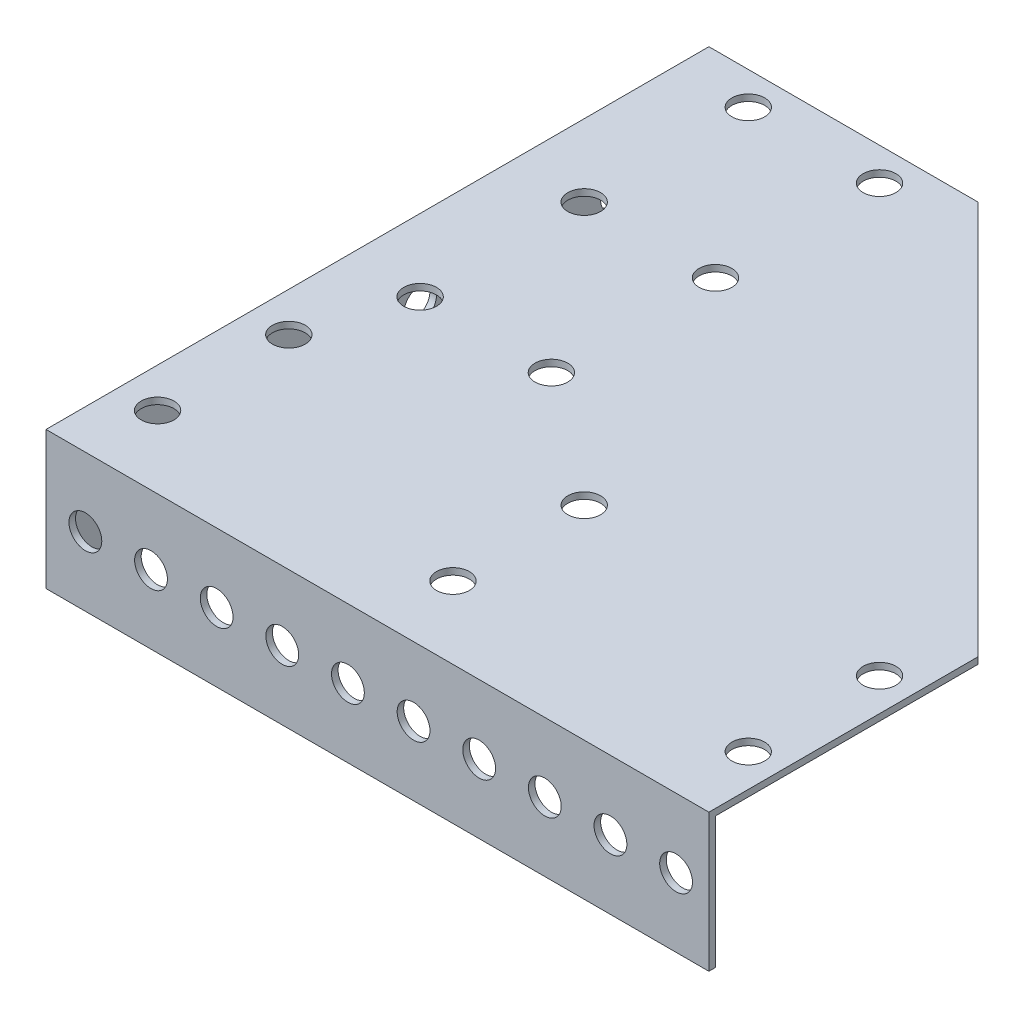
SolidWorks part; units mm, degrees
ref_plane "Front Plane" through (0, 0, 0) normal (0, 0, 1) x (1, 0, 0)
ref_plane "Top Plane" through (0, 0, 0) normal (0, 1, 0) x (1, 0, 0)
ref_plane "Right Plane" through (0, 0, 0) normal (1, 0, 0) x (0, 0, -1)
sketch "Sketch1" plane through (0, 0, 0) normal (0, 1, 0) x (1, 0, 0)
  line L0 (0, 0) -> (0, -100)
  line L1 (0, -100) -> (100, -100)
  line L2 (100, -100) -> (100, -60)
  line L3 (100, -60) -> (40, 0)
  line L4 (40, 0) -> (0, 0)
  line L5 (40, 0) -> (40, -60) construction
  line L6 (40, -60) -> (100, -60) construction
  line L7 (40, -5) -> (20, -5) construction
  line L8 (20, -5) -> (0, -5) construction
  line L9 (40, -30) -> (0, -30) construction
  line L10 (50, -80) -> (50, -60) construction
  line L11 (40, -5) -> (40, -30) construction
  line L12 (40, -17.5) -> (0, -17.5) construction
  line L13 (100, -80) -> (50, -80) construction
  line L14 (50, -100) -> (50, -80) construction
  circle A0 centre (10, -5) radius 2.5
  circle A1 centre (30, -5) radius 2.5
  circle A6 centre (30, -55) radius 2.5
  circle A7 centre (10, -55) radius 2.5
  circle A10 centre (30, -30) radius 2.5
  circle A11 centre (10, -30) radius 2.5
  circle A14 centre (50, -70) radius 2.5
  circle A15 centre (50, -90) radius 2.5
  circle A16 centre (95, -70) radius 2.5
  circle A17 centre (95, -90) radius 2.5
  circle A18 centre (5, -70) radius 2.5
  circle A19 centre (5, -90) radius 2.5
  dimension "D4" = 5
  dimension "D6" = 5
  dimension "D1" = 40
  dimension "D2" = 40
  dimension "D3" = 100
  dimension "D5" = 5
extrude "Boss-Extrude1" add sketch "Sketch1" along normal blind 1
sketch "Sketch2" plane through (0, 0, 0) normal (-1, 0, 0) x (0, 0, 1)
  line L0 (0, 0) -> (100, 0) construction
  line L9 (100, 1) -> (0, 1)
  line L10 (100, 1) -> (100, -20)
  line L11 (100, -20) -> (0, -20)
  line L12 (0, 1) -> (0, -20)
  line L13 (0, 1) -> (0, 0) construction
  line L14 (5, -10) -> (15, -10) construction
  line L15 (5, -10) -> (0, -10) construction
  line L16 (75, -10) -> (80, -10) construction
  line L17 (80, 0) -> (80, -20) construction
  circle A0 centre (5, -10) radius 2.5
  circle A1 centre (15, -10) radius 2.5
  circle A2 centre (25, -10) radius 2.5
  circle A3 centre (35, -10) radius 2.5
  circle A4 centre (45, -10) radius 2.5
  circle A5 centre (55, -10) radius 2.5
  circle A6 centre (65, -10) radius 2.5
  circle A7 centre (75, -10) radius 2.5
  dimension "D4" = 5
  dimension "D1" = 20
  dimension "D3" = 10
  dimension "D5" = 20
  dimension "D2" = 8
extrude "Boss-Extrude2" add sketch "Sketch2" along normal blind 1
sketch "Sketch3" plane through (0, 0, 100) normal (0, 0, 1) x (1, 0, 0)
  line L0 (95, -9.5) -> (85, -9.5) construction
  line L1 (100, 1) -> (-1, 1)
  line L2 (100, 1) -> (100, -20)
  line L3 (100, -20) -> (-1, -20)
  line L4 (-1, 1) -> (-1, -20)
  line L5 (-1, -20) -> (-1, 1) construction
  line L6 (-1, -20) -> (0, -20) construction
  line L7 (95, -9.5) -> (100, -9.5) construction
  line L8 (5, -9.5) -> (0, -9.5) construction
  line L9 (0, -20) -> (0, 0) construction
  circle A0 centre (95, -9.5) radius 2.5
  circle A1 centre (85, -9.5) radius 2.5
  circle A2 centre (75, -9.5) radius 2.5
  circle A3 centre (65, -9.5) radius 2.5
  circle A4 centre (55, -9.5) radius 2.5
  circle A5 centre (45, -9.5) radius 2.5
  circle A6 centre (35, -9.5) radius 2.5
  circle A7 centre (25, -9.5) radius 2.5
  circle A8 centre (15, -9.5) radius 2.5
  circle A9 centre (5, -9.5) radius 2.5
  dimension "D3" = 5
  dimension "D2" = 10
  dimension "D1" = 10
extrude "Boss-Extrude5" add sketch "Sketch3" along normal blind 1
